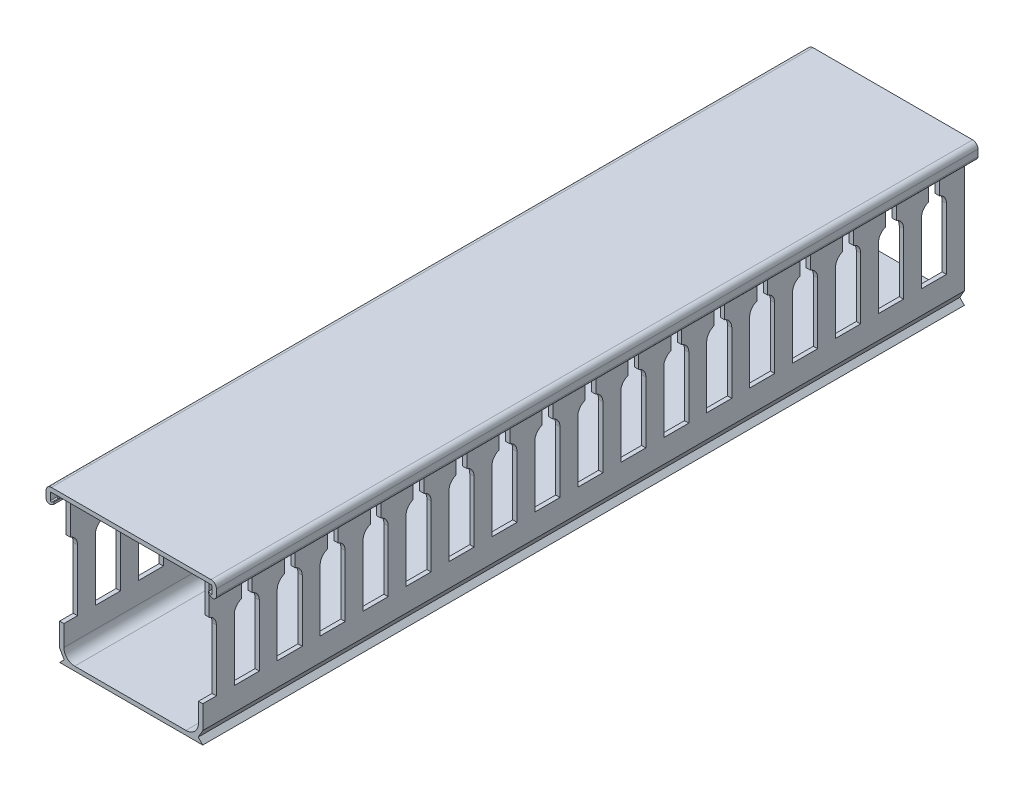
SolidWorks part; units mm, degrees
ref_plane "Front Plane" through (0, 0, 0) normal (0, 0, 1) x (1, 0, 0)
ref_plane "Top Plane" through (0, 0, 0) normal (0, 1, 0) x (1, 0, 0)
ref_plane "Right Plane" through (0, 0, 0) normal (1, 0, 0) x (0, 0, -1)
sketch "Sketch1" plane through (0, 0, 0) normal (0, 0, 1) x (1, 0, 0)
  line L0 (-20, 0) -> (20, 0)
  line L1 (-20, 3.5) -> (-20, 38.546)
  line L2 (-20, 0) -> (-18.7189, 1.2811)
  line L3 (-18.7189, 1.2811) -> (-20, 3.5)
  line L4 (-22.4196, 37.589) -> (-20.381, 38.766)
  line L5 (0, 0) -> (0, -17.0643) construction
  line L6 (22.4196, 37.589) -> (22.5, 37.889)
  line L7 (22.4196, 37.589) -> (20.381, 38.766)
  line L8 (20, 3.5) -> (20, 38.546)
  line L9 (18.7189, 1.2811) -> (20, 3.5)
  line L10 (-22.4196, 37.589) -> (-22.5, 37.889)
  line L11 (20, 0) -> (18.7189, 1.2811)
  line L12 (-18.8, 4.2) -> (-18.8, 38.546)
  line L13 (18.8, 3.5) -> (18.8, 38.546) construction
  line L14 (-17.2865, 1.2) -> (20, 1.2) construction
  line L15 (-15.8, 1.2) -> (15.3, 1.2)
  line L16 (18.8, 4.7) -> (18.8, 38.546)
  line L17 (-17.2865, 1.2) -> (-18.8, 3.8215) construction
  line L18 (-17.2865, 1.2) -> (-17.2865, 1.2) construction
  line L19 (-18.8, 3.8215) -> (-18.8, 38.546) construction
  arc A0 (-22.5, 37.889) -> (-21.2623, 39.5936) centre (-17.1014, 35.2708) cw
  arc A1 (22.5, 37.889) -> (21.2623, 39.5936) centre (17.1014, 35.2708) ccw
  arc A2 (20.381, 38.766) -> (20, 38.546) centre (20.254, 38.546) ccw
  arc A3 (-21.2623, 39.5936) -> (-18.8, 38.546) centre (-20.254, 38.546) cw
  arc A4 (21.2623, 39.5936) -> (18.8, 38.546) centre (20.254, 38.546) ccw
  arc A5 (-15.8, 1.2) -> (-18.8, 4.2) centre (-15.8, 4.2) cw
  arc A6 (-20.381, 38.766) -> (-20, 38.546) centre (-20.254, 38.546) cw
  arc A7 (15.3, 1.2) -> (18.8, 4.7) centre (15.3, 4.7) ccw
  arc A8 (-20.981, 39.8052) -> (-18.8, 38.546) centre (-20.254, 38.546) cw construction
  arc A9 (20.981, 39.8052) -> (18.8, 38.546) centre (20.254, 38.546) ccw construction
  dimension "D1" = 0.3
  dimension "D2" = 6
  dimension "D3" = 60
  dimension "D5" = 0.254
  dimension "D6" = 1.2
  dimension "D11" = 3
  dimension "D13" = 3.5
  dimension "D14" = 40
  dimension "D7" = 45
  dimension "D8" = 30
  dimension "D4" = 75
  dimension "D9" = 3.5
  dimension "D10" = 2.5
  dimension "D12" = 40
extrude "Boss-Extrude2" add sketch "Sketch1" along normal mid plane 1000 contours L0 L11 L9 L8 A2 L7 L6 A1 A4 L16 A7 L15 A5 L12 A3 A0 L10 L4 A6 L1 L3 L2
sketch "Sketch2" plane through (0, 0, 0) normal (1, 0, 0) x (0, 0, -1)
  line L0 (490, 30) -> (490, 40)
  line L1 (-500, 0) -> (500, 0) construction
  line L2 (500, 3.5) -> (500, 38.546) construction
  line L3 (488, 10) -> (495, 10)
  line L4 (495, 10) -> (495, 27.1716)
  line L6 (490, 40) -> (493, 40)
  line L7 (493, 30) -> (493, 40)
  line L8 (488, 10) -> (488, 27.1716)
  line L10 (500, 40) -> (-500, 40) construction
  arc A0 (495, 27.1716) -> (493, 30) centre (492, 27.1716) ccw
  arc A1 (488, 27.1716) -> (490, 30) centre (491, 27.1716) cw
  point P22 (491.5, 10)
  point P23 (491.5, 40)
  dimension "D1" = 3
  dimension "D2" = 10
  dimension "D3" = 10
  dimension "D4" = 7
  dimension "D5" = 5
  dimension "D6" = 3
extrude "Cut-Extrude1" cut sketch "Sketch2" against normal blind 82.296 and the other way blind 151.13
pattern_linear "LPattern1" count 83 spacing 12 along (0, 0, 1) of "Cut-Extrude1"
sketch "Sketch3" plane through (0, 0, -500) normal (0, 0, 1) x (1, 0, 0)
  line L0 (-22.6, 37.9) -> (-22.6, 39.7) construction
  line L1 (-22.6, 37.8781) -> (-22.6, 39.7)
  line L2 (22.3, 40) -> (-22.3, 40)
  line L4 (22.6, 37.8781) -> (22.6, 39.7)
  line L5 (22.6, 37.9) -> (22.6, 39.7) construction
  line L6 (22.3, 41.2) -> (-22.3, 41.2)
  line L7 (-22.3, 37.034) -> (-21.6, 37.4381)
  line L8 (-21.6, 37.4381) -> (-21.6, 38.0155)
  line L9 (-23.8, 37.9) -> (-23.8, 39.7)
  line L10 (-21.6, 38.0155) -> (-22.219, 37.6581)
  line L12 (22.3, 37.034) -> (21.6, 37.4381)
  line L14 (21.6, 38.0155) -> (22.219, 37.6581)
  line L15 (23.8, 37.9) -> (23.8, 39.7)
  line L16 (21.6, 37.4381) -> (21.6, 38.0155)
  arc A0 (-23.8, 37.9) -> (-22.3, 37.034) centre (-22.8, 37.9) ccw
  arc A1 (-22.6, 37.8781) -> (-22.219, 37.6581) centre (-22.346, 37.8781) ccw
  arc A2 (22.3, 37.034) -> (23.8, 37.9) centre (22.8, 37.9) ccw
  arc A3 (-22.3, 41.2) -> (-23.8, 39.7) centre (-22.3, 39.7) ccw
  arc A4 (-22.3, 40) -> (-22.6, 39.7) centre (-22.3, 39.7) ccw
  arc A5 (22.3, 41.2) -> (23.8, 39.7) centre (22.3, 39.7) cw
  arc A6 (22.3, 40) -> (22.6, 39.7) centre (22.3, 39.7) cw
  arc A7 (22.6, 37.8781) -> (22.219, 37.6581) centre (22.346, 37.8781) cw
  arc A9 (-18.8, 38.546) -> (-21.2623, 39.5936) centre (-20.254, 38.546) ccw construction
  point P35 (0, 40)
  dimension "D2" = 2.2
  dimension "D3" = 0.254
  dimension "D4" = 2.2
  dimension "D5" = 1.5
  dimension "D7" = 4.3
  dimension "D12" = 1
  dimension "D6" = 60
  dimension "D8" = 60
  dimension "D9" = 0.5
  dimension "D11" = 0.1
  dimension "D10" = 1.2
extrude "Boss-Extrude3" add sketch "Sketch3" along normal up to vertex separate body
sketch "Sketch4" plane through (0, 0, 500) normal (0, 0, 1) x (1, 0, 0)
  line L1 (-27.5029, 42.7426) -> (26.9563, 42.7426)
  line L2 (-27.5029, 42.7426) -> (-27.5029, -2.6712)
  line L3 (-27.5029, -2.6712) -> (26.9563, -2.6712)
  line L4 (26.9563, 42.7426) -> (26.9563, -2.6712)
extrude "Cut-Extrude2" cut sketch "Sketch4" against normal blind 787.2
